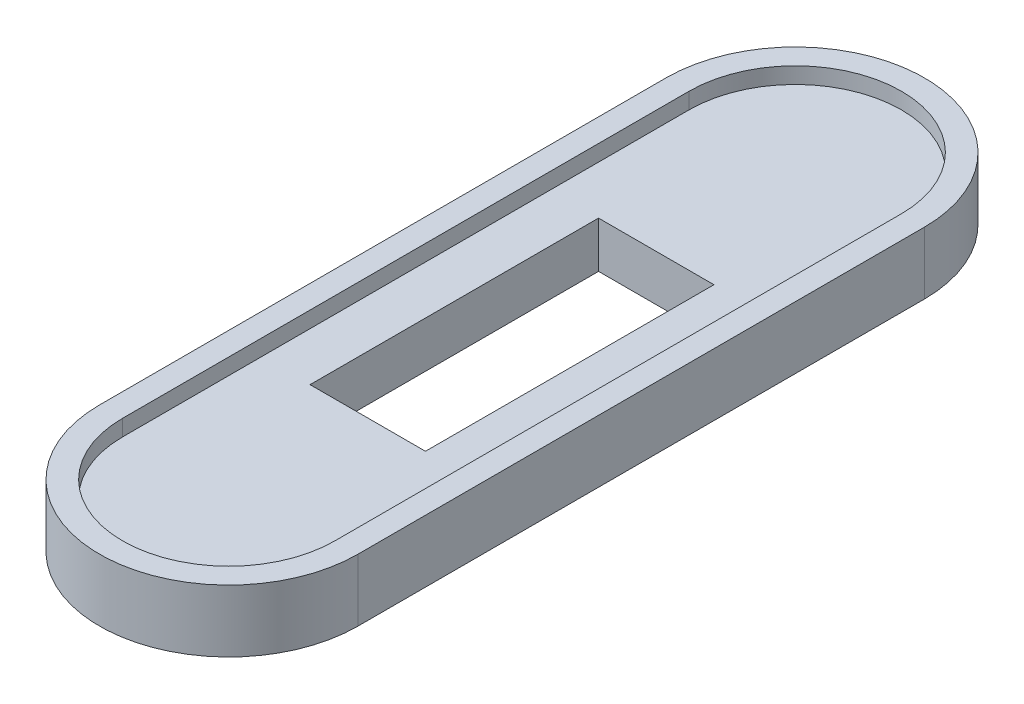
SolidWorks part; units mm, degrees
ref_plane "Front Plane" through (0, 0, 0) normal (0, 0, 1) x (1, 0, 0)
ref_plane "Top Plane" through (0, 0, 0) normal (0, 1, 0) x (1, 0, 0)
ref_plane "Right Plane" through (0, 0, 0) normal (1, 0, 0) x (0, 0, -1)
sketch "Sketch1" plane through (0, 0, 0) normal (0, 1, 0) x (1, 0, 0)
  line L1 (0, 0) -> (18.4, 0) construction
  line L2 (0, 0) -> (0, 49.1)
  line L3 (0, 49.1) -> (18.4, 49.1) construction
  line L4 (18.4, 0) -> (18.4, 49.1)
  arc A0 (0, 49.1) -> (18.4, 49.1) centre (9.2, 49.1) cw
  arc A1 (0, 0) -> (18.4, 0) centre (9.2, 0) ccw
extrude "Extrude-Thin1" add sketch "Sketch1" along normal blind 1.4 thin thin type one direction wall 2
sketch "Sketch2" plane through (0, 0, 0) normal (0, -1, 0) x (1, 0, 0)
  line L0 (-2, 0) -> (-2, -49.1)
  line L1 (20.4, -49.1) -> (20.4, 0)
  line L2 (9.2, 11.2) -> (9.2, -24.55) construction
  line L3 (9.2, -24.55) -> (-2, -24.55) construction
  line L4 (14.2, -37.05) -> (14.2, -12.05)
  line L5 (14.2, -37.05) -> (4.2, -37.05)
  line L6 (14.2, -12.05) -> (4.2, -12.05)
  line L7 (4.2, -37.05) -> (4.2, -12.05)
  line L8 (14.2, -37.05) -> (4.2, -12.05) construction
  line L9 (14.2, -12.05) -> (4.2, -37.05) construction
  arc A0 (-2, -49.1) -> (20.4, -49.1) centre (9.2, -49.1) ccw
  arc A1 (20.4, 0) -> (-2, 0) centre (9.2, 0) ccw
extrude "Boss-Extrude1" add sketch "Sketch2" along normal blind 4
